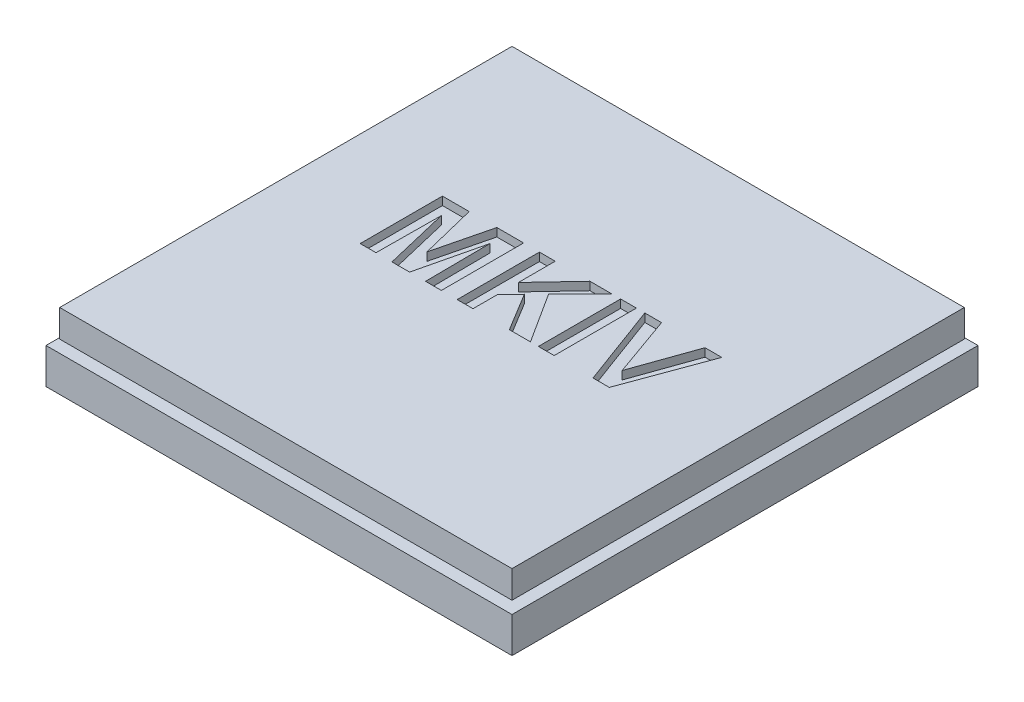
SolidWorks part; units mm, degrees
ref_plane "Спереди" through (0, 0, 0) normal (0, 0, 1) x (1, 0, 0)
ref_plane "Сверху" through (0, 0, 0) normal (0, 1, 0) x (1, 0, 0)
ref_plane "Справа" through (0, 0, 0) normal (1, 0, 0) x (0, 0, -1)
sketch "Sketch1" plane through (0, 0, 0) normal (0, 1, 0) x (1, 0, 0)
  line L1 (14.9, -14.9) -> (-14.9, -14.9)
  line L2 (14.9, -14.9) -> (14.9, 14.9)
  line L3 (14.9, 14.9) -> (-14.9, 14.9)
  line L4 (-14.9, -14.9) -> (-14.9, 14.9)
  line L5 (14.9, -14.9) -> (-14.9, 14.9) construction
  line L6 (14.9, 14.9) -> (-14.9, -14.9) construction
  point P0 (0, 0)
  dimension "D1" = 29.8
extrude "Boss-Extrude1" add sketch "Sketch1" along normal blind 3
sketch "Sketch2" plane through (0, 3, 0) normal (0, 1, 0) x (1, 0, 0)
  line L1 (16.5, -16.5) -> (-16.5, -16.5)
  line L2 (16.5, -16.5) -> (16.5, 16.5)
  line L3 (16.5, 16.5) -> (-16.5, 16.5)
  line L4 (-16.5, -16.5) -> (-16.5, 16.5)
  line L5 (16.5, -16.5) -> (-16.5, 16.5) construction
  line L6 (16.5, 16.5) -> (-16.5, -16.5) construction
  point P0 (0, 0)
  dimension "D1" = 33
extrude "Boss-Extrude2" add sketch "Sketch2" along normal blind 2
sketch "Sketch3" plane through (0, 5, 0) normal (0, 1, 0) x (1, 0, 0)
  line L0 (-16.5, -1.5) -> (16.5, -1.5) construction
  line L1 (-16.5, 16.5) -> (-16.5, -16.5) construction
  line L2 (16.5, -16.5) -> (16.5, 16.5) construction
  line L3 (-16.5, -16.5) -> (16.5, -16.5) construction
  text T0 "<b>MKIV</b>" font "Arial" height 6
  dimension "D1" = 15
sketch "Sketch5" plane through (0, 0, 0) normal (0, -1, 0) x (1, 0, 0)
  line L1 (-17, 17) -> (17, 17)
  line L2 (-17, 17) -> (-17, -17)
  line L3 (-17, -17) -> (17, -17)
  line L4 (17, 17) -> (17, -17)
  line L5 (-17, 17) -> (17, -17) construction
  line L6 (-17, -17) -> (17, 17) construction
  line L7 (-15.5, 15.5) -> (15.5, 15.5)
  line L8 (-15.5, 15.5) -> (-15.5, -15.5)
  line L9 (-15.5, -15.5) -> (15.5, -15.5)
  line L10 (15.5, 15.5) -> (15.5, -15.5)
  line L11 (-15.5, 15.5) -> (15.5, -15.5) construction
  line L12 (-15.5, -15.5) -> (15.5, 15.5) construction
  point P0 (0, 0)
  point P6 (0, 0)
  dimension "D1" = 31
  dimension "D2" = 34
extrude "Boss-Extrude4" add sketch "Sketch5" against normal offset from surface (2.6 mm away) 0.4 separate body up to face at (0, 3, 0)
chamfer "Chamfer1" distance 0.5 angle 60 4 edges at (14.9, 0, 0) (0, 0, 14.9) (-14.9, 0, 0) (0, 0, -14.9)
extrude "Cut-Extrude1" cut sketch "Sketch3" against normal blind 0.6
